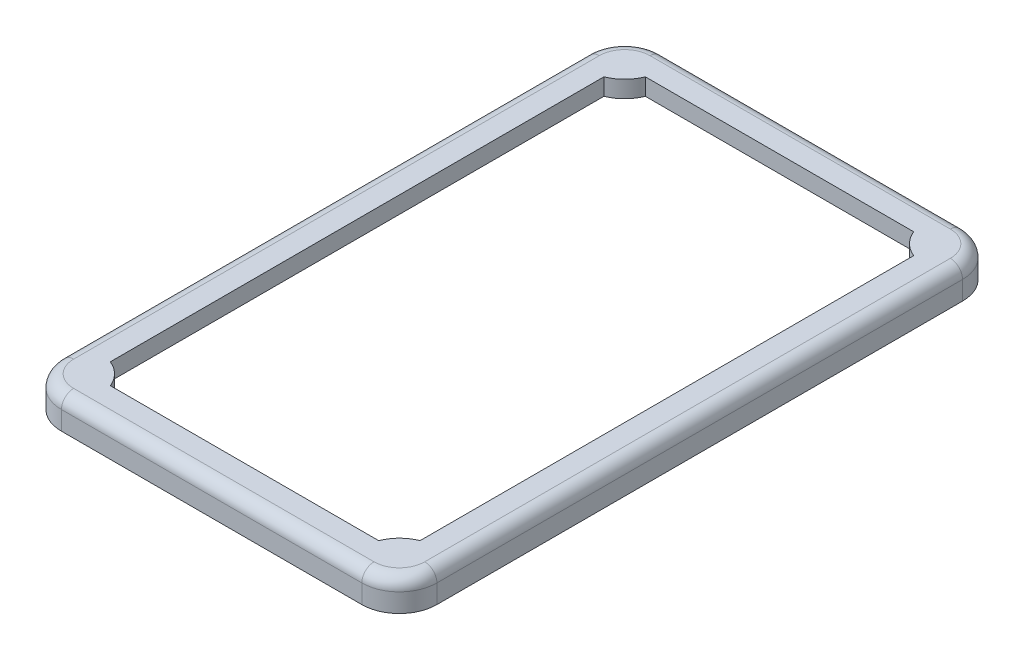
SolidWorks part; units mm, degrees
ref_plane "Front Plane" through (0, 0, 0) normal (0, 0, 1) x (1, 0, 0)
ref_plane "Top Plane" through (0, 0, 0) normal (0, 1, 0) x (1, 0, 0)
ref_plane "Right Plane" through (0, 0, 0) normal (1, 0, 0) x (0, 0, -1)
sketch "Sketch1" plane through (0, 0, 0) normal (0, 1, 0) x (1, 0, 0)
  line L1 (20, -32) -> (-20, -32)
  line L2 (20, -32) -> (20, 32)
  line L3 (20, 32) -> (-20, 32)
  line L4 (-20, -32) -> (-20, 32)
  line L5 (20, -32) -> (-20, 32) construction
  line L6 (20, 32) -> (-20, -32) construction
  line L7 (18, -30) -> (-18, -30)
  line L8 (18, -30) -> (18, 30)
  line L9 (18, 30) -> (-18, 30)
  line L10 (-18, -30) -> (-18, 30)
  line L11 (18, -30) -> (-18, 30) construction
  line L12 (18, 30) -> (-18, -30) construction
  point P0 (0, 0)
  point P6 (0, 0)
  dimension "D1" = 40
  dimension "D2" = 64
  dimension "D3" = 2
  dimension "D4" = 2
extrude "Boss-Extrude1" add sketch "Sketch1" along normal blind 3.3
sketch "Sketch3" plane through (0, 3.3, 0) normal (0, 1, 0) x (1, 0, 0)
  line L0 (-14.2919, -28.5) -> (14.2919, -28.5)
  line L1 (-18, 26) -> (-18, 30)
  line L2 (-18, 30) -> (-14, 30)
  line L4 (0, 27.3879) -> (0, -1.4953) construction
  line L5 (-16.5, 26.2919) -> (-16.5, -26.2919)
  line L6 (-17, 0) -> (17, 0) construction
  line L7 (-14.2919, 28.5) -> (14.2919, 28.5)
  line L9 (-18, 30) -> (-15.1716, 27.1716) construction
  line L11 (-18, 30) -> (-18, 26)
  line L12 (-14, 30) -> (-18, 30)
  line L13 (18, 30) -> (15.1716, 27.1716) construction
  line L14 (14, 30) -> (18, 30)
  line L15 (18, 30) -> (18, 26)
  line L16 (18, 30) -> (14, 30)
  line L17 (18, 26) -> (18, 30)
  line L18 (18, -30) -> (15.1716, -27.1716) construction
  line L19 (-18, -30) -> (-15.1716, -27.1716) construction
  line L20 (18, -26) -> (18, -30)
  line L21 (18, -30) -> (14, -30)
  line L22 (18, -30) -> (18, -26)
  line L23 (14, -30) -> (18, -30)
  line L24 (-14, -30) -> (-18, -30)
  line L25 (-18, -30) -> (-18, -26)
  line L26 (-18, -30) -> (-14, -30)
  line L27 (-18, -26) -> (-18, -30)
  line L28 (-18, 30) -> (-18, -30) construction
  line L29 (18, 30) -> (-18, 30) construction
  line L30 (16.5, 26.2919) -> (16.5, -26.2919)
  circle A1 centre (-16.5858, 28.5858) radius 1 construction
  arc A4 (-18, 26) -> (-14, 30) centre (-18, 30) ccw
  arc A5 (18, 26) -> (14, 30) centre (18, 30) cw
  circle A6 centre (16.5858, 28.5858) radius 1 construction
  circle A7 centre (16.5858, -28.5858) radius 1 construction
  arc A8 (18, -26) -> (14, -30) centre (18, -30) ccw
  arc A9 (-18, -26) -> (-14, -30) centre (-18, -30) cw
  circle A10 centre (-16.5858, -28.5858) radius 1 construction
  point P3 (-18, 0)
  point P11 (0, 30)
  line M105 (18, -30) -> (-18, -30)
  line M106 (-18, -30) -> (-18, 30)
  line M107 (-18, 30) -> (18, 30)
  line M108 (18, 30) -> (18, -30)
  dimension "D2" = 2
  dimension "D1" = 4
  dimension "D3" = 1.5
  dimension "D4" = 1.5
extrude "Boss-Extrude2" add sketch "Sketch3" against normal offset from surface (1.8 mm away) 1.5 contours A4 A1 M106 M107 | A6 A5 M108 M107 | A8 L21 A7 M108 | A9 L24 A10 M106 | A9 L5 A4 M106 | L0 A9 A8 M105 | A8 A5 L30 M108 | L7 A5 A4 M107
fillet "Fillet1" radius 4 4 edges at (20, 1.65, -32) (-20, 1.65, -32) (20, 1.65, 32) (-20, 1.65, 32)
hole_wizard "M2.2x0.45 Tapped Hole1" positions "Sketch4" profile "Sketch5" tap size "M2.2x0.45" standard "ANSI Metric"
sketch "Sketch4" plane through (0, 1.5, 0) normal (0, 1, 0) x (1, 0, 0)
  line L0 (-18, -30) -> (-15.1716, -27.1716) construction
  line L1 (18, 30) -> (15.1716, 27.1716) construction
  point P0 (-16.5858, -28.5858)
  point P7 (16.5858, -28.5858)
  point P13 (-16.5858, 28.5858)
  point P16 (16.5858, 28.5858)
sketch "Sketch5" plane through (-16.5858, 1.5, 28.5858) normal (1, 0, 0) x (0, 0, -1)
  line L0 (0, 0) -> (0, 1.7258)
  line L1 (0, 1.7258) -> (0.875, 1.2)
  line L2 (0.875, 1.2) -> (0.875, 0.25)
  line L3 (0.875, 0.25) -> (1.125, 0)
  line L5 (1.125, 0) -> (0, 0)
  line L6 (-0.875, 0.25) -> (-1.125, 0) construction
  line L10 (0, 1.7258) -> (-0.875, 1.2) construction
  line L11 (0, -6.35) -> (0, 107.95) construction
  dimension "Tap Drill Dia." = 1.75
  dimension "Tap Drill Depth" = 1.2
  dimension "Near C'Sink Dia." = 2.25
  dimension "Near C'Sink Angle" = 90
  dimension "Drill Angle" = 118
fillet "Fillet3" radius 1.3 8 edges at (-18.8284, 3.3, 30.8284) (-20, 3.3, 0) (-18.8284, 3.3, -30.8284) (0, 3.3, -32) (18.8284, 3.3, -30.8284) (20, 3.3, 0) (18.8284, 3.3, 30.8284) (0, 3.3, 32)
